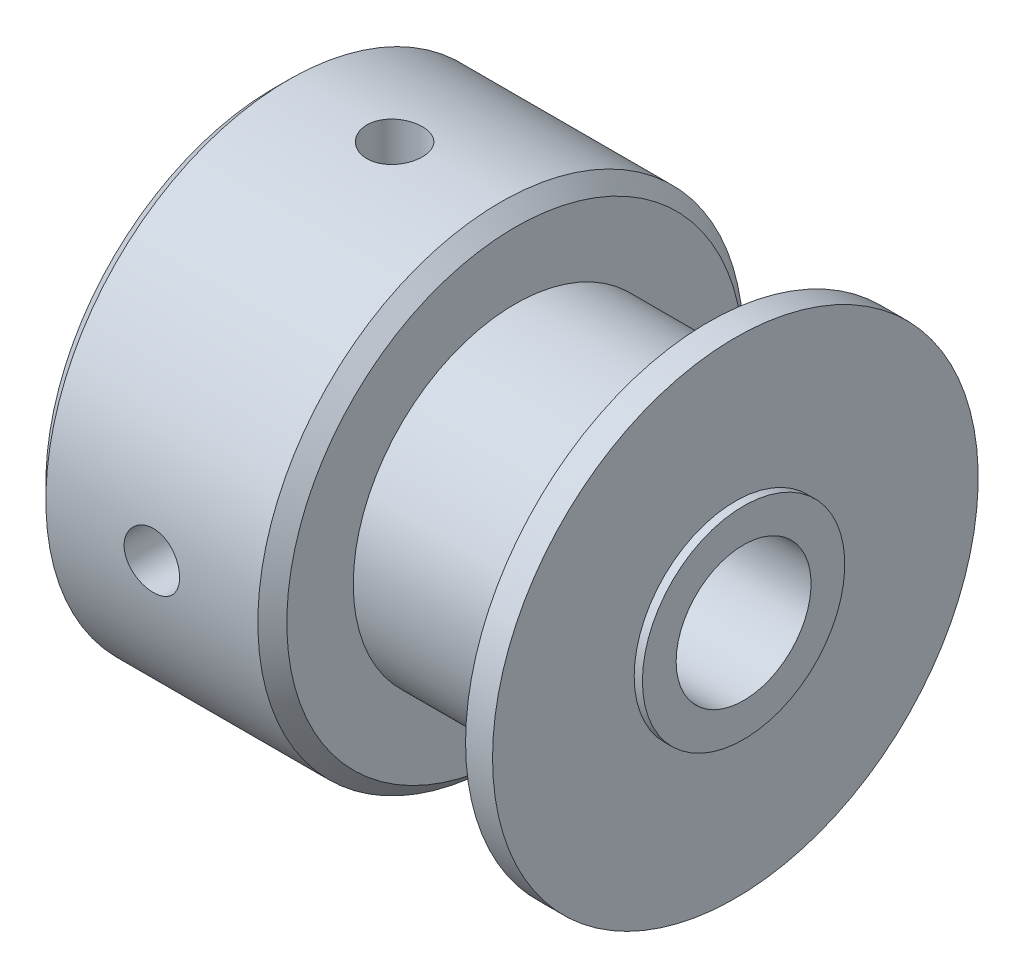
SolidWorks part; units mm, degrees
ref_plane "Front Plane" through (0, 0, 0) normal (0, 0, 1) x (1, 0, 0)
ref_plane "Top Plane" through (0, 0, 0) normal (0, 1, 0) x (1, 0, 0)
ref_plane "Right Plane" through (0, 0, 0) normal (1, 0, 0) x (0, 0, -1)
sketch "Sketch2" plane through (0, 0, 0) normal (0, 0, 1) x (1, 0, 0)
  line L1 (-7.1374, 0) -> (8.7, 0) construction
  line L2 (0, -1.094) -> (0, 4.8952) construction
  line L3 (-8.7, 2.5) -> (8.7, 2.5)
  line L4 (-8.7, 2.5) -> (-8.7, 3.75)
  line L5 (-8.7, 3.75) -> (0.2322, 3.75)
  line L6 (0.2322, 3.75) -> (0.2322, 6)
  line L7 (0.2322, 6) -> (7.395, 6)
  line L8 (7.395, 6) -> (7.395, 3.75)
  line L9 (7.395, 3.75) -> (8.7, 3.75)
  line L10 (8.7, 3.75) -> (8.7, 2.5)
  dimension "D3" = 1.305
  dimension "D4" = 7.5
  dimension "Dimension [E]" = 17.4
  dimension "Bore [A]" = 5
  dimension "Width [DD]" = 7.1628
  dimension "Outside Diameter [B]" = 12
revolve "Base Body" add sketch "Sketch2" angle 360 about L1
sketch "Sketch3" plane through (0, 0, 0) normal (0, 1, 0) x (1, 0, 0)
  line L0 (0.2322, 3.75) -> (-8.7, 3.75) construction
  line L1 (0.2322, 3.75) -> (-8.7, 3.75)
  line L2 (0.2322, 3.75) -> (0.2322, 8.4628)
  line L3 (-0.305, 9) -> (-8.1628, 9)
  line L4 (-8.7, 3.75) -> (-8.7, 8.4628)
  line L5 (0.2322, 6) -> (0.2322, -6) construction
  line L6 (-8.7, 8.4628) -> (-8.1628, 9)
  line L7 (0, 0) -> (-8.7, 0) construction
  line L8 (-8.7, 3.75) -> (-8.7, -3.75) construction
  line L9 (-4.2339, 3.75) -> (-4.2339, 6.096) construction
  line L10 (0.2322, 8.4628) -> (-0.305, 9)
  line L11 (-8.7, 8.4628) -> (-8.7, 9) construction
  line L12 (-8.7, 9) -> (-8.1628, 9) construction
  dimension "Hub Diameter [F]" = 18
  dimension "D2" = 0.5372
revolve "Hub" add sketch "Sketch3" angle 360 about L7
sketch "Sketch4" plane through (0, 0, 0) normal (0, 1, 0) x (1, 0, 0)
  line L0 (7.395, -6) -> (7.395, 6) construction
  line L1 (7.395, 3.75) -> (8.395, 3.75)
  line L2 (7.395, 3.75) -> (7.395, 9)
  line L3 (0, 0) -> (7.0313, 0) construction
  line L4 (7.395, 9) -> (8.395, 9)
  line L5 (8.395, 3.75) -> (8.395, 9)
  line L6 (8.7, 3.75) -> (7.395, 3.75) construction
  dimension "D2" = 9
  dimension "D1" = 1
revolve "Flange" add sketch "Sketch4" angle 360 about L3
sketch "Sketch5" plane through (0, 0, 0) normal (0, 1, 0) x (1, 0, 0)
  line L0 (-4.2339, 9) -> (-4.2339, -9) construction
  line L1 (-8.1628, -9) -> (-0.305, -9) construction
  line L2 (-0.305, 9) -> (-8.1628, 9) construction
  circle A0 centre (-4.2339, 0) radius 1.0287
  dimension "Diameter [DI]" = 2.0574
extrude "Set Screws" cut sketch "Sketch5" along normal blind 10
cosmetic thread "Cosmetic Thread2" parameters "D2"=2.1603
pattern_circular "CirPattern1" count 2 every 90 about axis through (-7.1374, 0, 0) along (1, 0, 0) of "Set Screws"
cosmetic thread "Cosmetic Thread1" parameters "D2"=2.1603
equation "\"D4@Sketch2\" = \"Bore [A]@Sketch2\"*1.5"
equation "\"D3@Sketch2\" = \"Dimension [E]@Sketch2\"*.075"
equation "\"D2@Sketch3\" = \"Width [DD]@Sketch2\"*.075"
equation "\"D2@Cosmetic Thread2\" = \"Diameter [DI]@Sketch5\"*1.05"
equation "\"D2@Cosmetic Thread1\" = \"D2@Cosmetic Thread2\""
